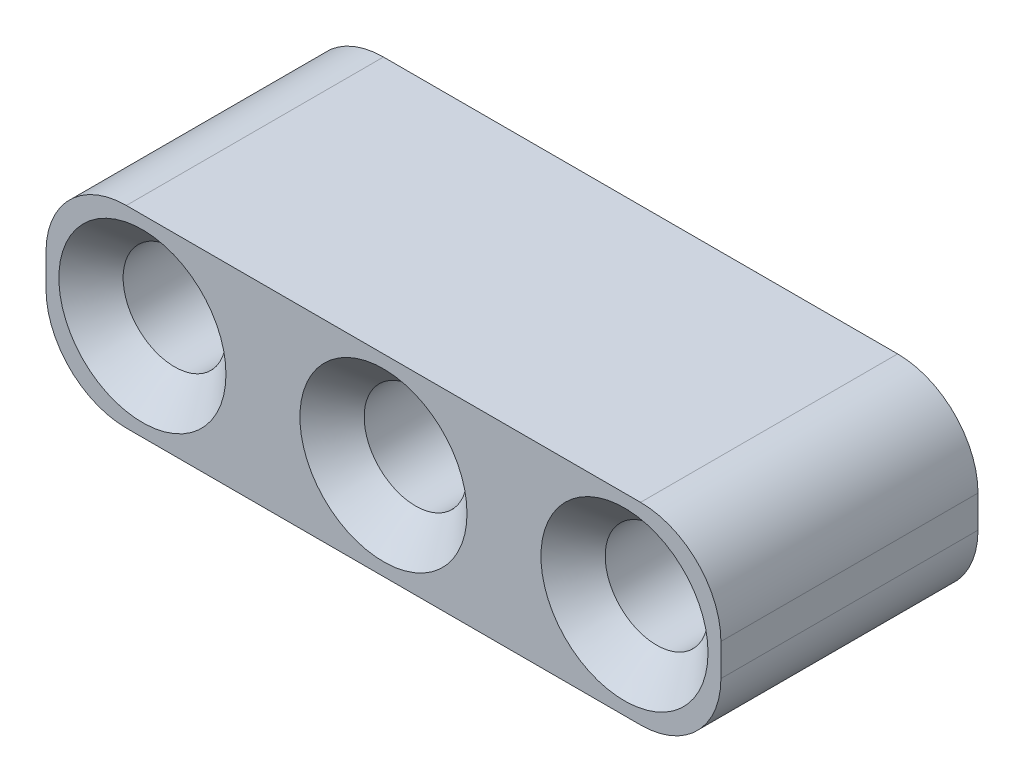
SolidWorks part; units mm, degrees
ref_plane "Front Plane" through (0, 0, 0) normal (0, 0, 1) x (1, 0, 0)
ref_plane "Top Plane" through (0, 0, 0) normal (0, 1, 0) x (1, 0, 0)
ref_plane "Right Plane" through (0, 0, 0) normal (1, 0, 0) x (0, 0, -1)
sketch "Sketch1" plane through (0, 0, 0) normal (0, 0, 1) x (1, 0, 0)
  line L1 (-0.5, 3) -> (15.5, 3)
  line L2 (-3, 0.5) -> (-3, -0.5)
  line L3 (-0.5, -3) -> (15.5, -3)
  line L4 (18, 0.5) -> (18, -0.5)
  circle A0 centre (0, 0) radius 1.6
  arc A1 (15.5, -3) -> (18, -0.5) centre (15.5, -0.5) ccw
  arc A2 (15.5, 3) -> (18, 0.5) centre (15.5, 0.5) cw
  arc A3 (-3, -0.5) -> (-0.5, -3) centre (-0.5, -0.5) ccw
  arc A4 (-0.5, 3) -> (-3, 0.5) centre (-0.5, 0.5) ccw
  circle A5 centre (7.5, 0) radius 1.6
  circle A6 centre (15, 0) radius 1.6
  point P8 (-3, 0)
  point P14 (-3, -3)
  point P17 (-3, 3)
  dimension "D1" = 3.2
  dimension "D4" = 2.5
  dimension "D2" = 6
  dimension "D3" = 3
  dimension "D6" = 7.5
  dimension "D5" = 3
extrude "Boss-Extrude1" add sketch "Sketch1" along normal blind 8
chamfer "Chamfer1" distance 1 angle 45 6 edges at (16.6, 0, 0) (16.6, 0, 8) (9.1, 0, 0) (9.1, 0, 8) (1.6, 0, 0) (1.6, 0, 8)
